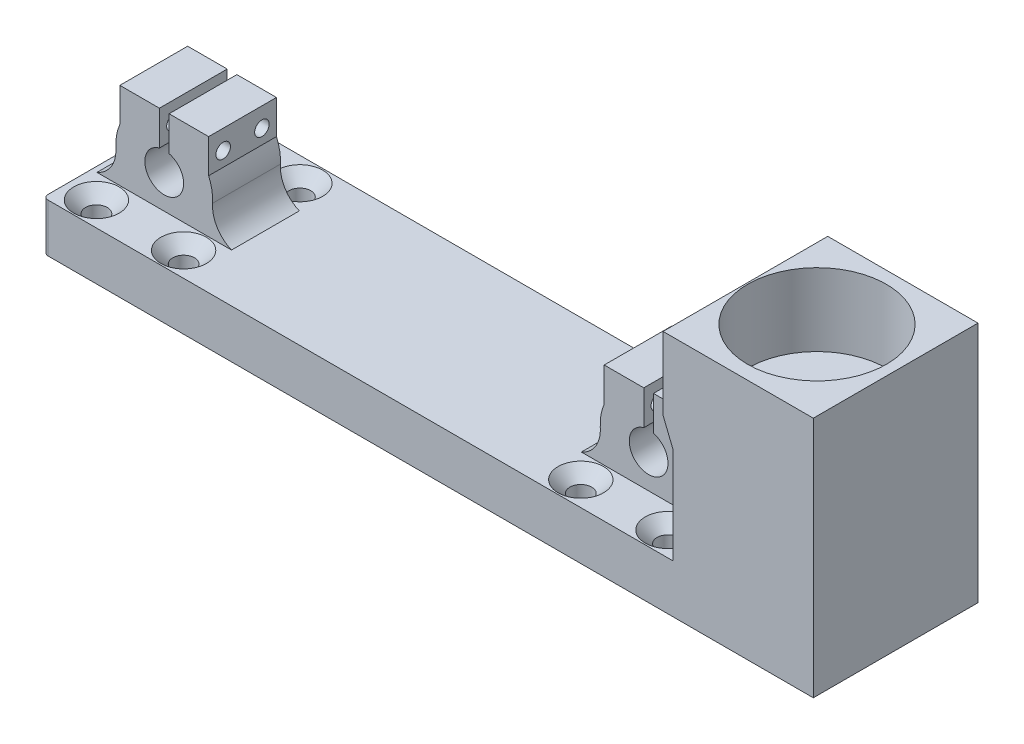
SolidWorks part; units mm, degrees
ref_plane "Front Plane" through (0, 0, 0) normal (0, 0, 1) x (1, 0, 0)
ref_plane "Top Plane" through (0, 0, 0) normal (0, 1, 0) x (1, 0, 0)
ref_plane "Right Plane" through (0, 0, 0) normal (1, 0, 0) x (0, 0, -1)
sketch "Sketch1" plane through (0, 0, 0) normal (0, 1, 0) x (1, 0, 0)
  line B0 (-24, -29) -> (6, -29)
  line B1 (6, 5) -> (6, -29)
  line B2 (-24, 5) -> (-24, -29)
  line B3 (-24, 5) -> (6, 5)
  circle B4 centre (0, -24) radius 2
  circle B5 centre (-18, -24) radius 2
  circle B6 centre (-18, 0) radius 2
  circle B7 centre (0, 0) radius 2
sketch_block_instance "Block-LinearBearing-1"
sketch_block "Block-LinearBearing"
sketch "Sketch2" plane through (0, 0, 0) normal (0, 1, 0) x (1, 0, 0)
  line L0 (-24, -29) -> (6, -29) construction
  line L1 (6, 5) -> (6, -29) construction
  line L2 (-24, 5) -> (-24, -29) construction
  line L3 (-24, 5) -> (6, 5) construction
  line L4 (-24, -29) -> (6, -29)
  line L5 (6, 5) -> (6, -29)
  line L6 (-24, 5) -> (-24, -29)
  line L7 (-24, 5) -> (6, 5)
  line L8 (6, 5) -> (41, 5)
  line L9 (41, 5) -> (41, -29)
  line L10 (41, -29) -> (6, -29)
  circle A0 centre (0, 0) radius 2 construction
  circle A1 centre (-18, 0) radius 2 construction
  circle A2 centre (-18, -24) radius 2 construction
  circle A3 centre (0, -24) radius 2 construction
  circle A4 centre (0, 0) radius 2
  circle A5 centre (-18, 0) radius 2
  circle A6 centre (-18, -24) radius 2
  circle A7 centre (0, -24) radius 2
  dimension "D1" = 35
extrude "Boss-Extrude1" add sketch "Sketch2" along normal blind 10 contours L10 L9 L8 L5 | L7 L6 L4 L5 A7 A6 A5 A4
fillet "Fillet1" radius 1 2 edges at (-24, 5, 29) (-24, 5, -5)
ref_plane "Plane1" through (0, 0, 19) normal (0, 0, 1) x (1, 0, 0)
sketch "Sketch3" plane through (0, 0, 19) normal (0, 0, 1) x (1, 0, 0)
  line L0 (-24, 0) -> (-24, 10) construction
  line L2 (-22.8852, 10) -> (4.8852, 10)
  line L3 (-9, 20.9227) -> (0.1652, 20.9227) construction
  line L4 (-9, 20.9227) -> (-18.1652, 20.9227) construction
  line L5 (-18.1652, 20.9227) -> (-18.1652, 27.9232)
  line L6 (-18.1652, 27.9232) -> (0.1652, 27.9232)
  line L7 (0.1652, 27.9232) -> (0.1652, 20.9227)
  circle A0 centre (-9, 16.9227) radius 4
  arc A2 (-19.0471, 16.9227) -> (-22.8852, 10) centre (-25.3926, 15.9155) cw
  arc A3 (1.0471, 16.9227) -> (4.8852, 10) centre (7.3926, 15.9155) ccw
  arc A4 (0.9741, 16.2033) -> (0.1652, 20.9227) centre (-9, 16.9227) ccw
  arc A5 (-18.1652, 20.9227) -> (-18.9741, 16.2033) centre (-9, 16.9227) ccw
  point P0 (-9, 10)
  dimension "D1" = 8
  dimension "D2" = 6
  dimension "D3" = 15
hole_wizard "CSK for M4 Flat Head Machine Screw1" positions "Sketch4" profile "Sketch5" countersink size "M4" standard "ANSI Metric" end condition up to next
sketch "Sketch4" plane through (0, 10, 0) normal (0, 1, 0) x (1, 0, 0)
  point P21 (-18, 0)
  point P24 (0, 0)
  point P27 (0, -24)
  point P30 (-18, -24)
sketch "Sketch5" plane through (-18, 10, 0) normal (1, 0, 0) x (0, 0, 1)
  line L0 (0, 0) -> (0, 10)
  line L1 (0, 10) -> (2.25, 10)
  line L2 (2.25, 10) -> (2.25, 2.45)
  line L3 (2.25, 2.45) -> (4.7, 0)
  line L5 (4.7, 0) -> (0, 0)
  line L6 (-2.25, 2.45) -> (-4.7, 0) construction
  line L11 (0, -6.35) -> (0, 107.95) construction
  dimension "Thru Hole Dia." = 4.5
  dimension "Thru Hole Depth" = 10
  dimension "Near C'Sink Dia." = 9.4
  dimension "Near C'Sink Angle" = 90
extrude "Boss-Extrude2" add sketch "Sketch3" against normal offset from surface (14 mm away) 10
hole_wizard "Ø3.0mm Dowel Hole1" positions "Sketch8" profile "Sketch9" hole size "Ø3.0" standard "ANSI Metric" end condition up to next
sketch "Sketch8" plane through (0.1652, 0, 0) normal (1, 0, 0) x (0, 0, -1)
  line L0 (-19, 27.9232) -> (-19, 20.9227) construction
  line L1 (-5, 20.9227) -> (-5, 27.9232) construction
  line L2 (-5, 27.9232) -> (-19, 27.9232) construction
  point P0 (-16, 23.9232)
  point P2 (-8, 23.9232)
  dimension "D1" = 3
  dimension "D2" = 3
  dimension "D3" = 4
  dimension "D4" = 4
sketch "Sketch9" plane through (0.1652, 23.9232, 16) normal (0, 1, 0) x (0, 0, -1)
  line L0 (0, 0) -> (0, 18.3303)
  line L1 (0, 18.3303) -> (1.5, 18.3303)
  line L2 (1.5, 18.3303) -> (1.5, 0)
  line L5 (1.5, 0) -> (0, 0)
  line L11 (0, -6.35) -> (0, 107.95) construction
  dimension "Thru Hole Dia." = 3
  dimension "Thru Hole Depth" = 18.3303
sketch "Sketch10" plane through (0, 0, 19) normal (0, 0, 1) x (1, 0, 0)
  line L0 (-10, 27.9232) -> (-8, 27.9232)
  line L1 (-18.1652, 27.9232) -> (0.1652, 27.9232) construction
  line L2 (-8, 27.9232) -> (-8, 20.7957)
  line L3 (-9, 27.9232) -> (-9, 20.9227)
  line L4 (-10, 27.9232) -> (-10, 20.7957)
  circle A0 centre (-9, 16.9227) radius 4 construction
  arc A1 (-8, 20.7957) -> (-10, 20.7957) centre (-9, 16.9227) ccw
  circle M5 centre (-9, 16.9227) radius 4
  line M13 (0.1652, 27.9232) -> (-18.1652, 27.9232)
  dimension "D1" = 1
extrude "Cut-Extrude1" cut sketch "Sketch10" against normal through all contours L0 L4 L3 M5 | L3 L2 M13 M5
mirror "Mirror11" about plane through (41, 10, 0) normal (1, 0, 0) of "Ø3.0mm Dowel Hole1", "Boss-Extrude1", "Boss-Extrude2", "Cut-Extrude1", "CSK for M4 Flat Head Machine Screw1"
hole_wizard "CSK for M3 Flat Head Machine Screw1" positions "Sketch13" profile "Sketch14" countersink size "M3" standard "ANSI Metric"
sketch "Sketch13" plane through (0, 0, -5) normal (0, 0, -1) x (-1, 0, 0)
  line L0 (23, 10) -> (-106, 10) construction
  line L3 (-41.5, 10) -> (-41.5, 0) construction
  line L4 (23, 0) -> (-106, 0) construction
  point P4 (-69.1148, 5)
  point P6 (-59.1148, 5)
  point P31 (-13.8852, 5)
  point P32 (-23.8852, 5)
  dimension "D1" = 5
  dimension "D2" = 8
  dimension "D3" = 10
  dimension "D4" = 5
sketch "Sketch14" plane through (69.1148, 5, -5) normal (1, 0, 0) x (0, 1, 0)
  line L0 (0, 0) -> (0, 11.0215)
  line L1 (0, 11.0215) -> (1.7, 10)
  line L2 (1.7, 10) -> (1.7, 1.45)
  line L3 (1.7, 1.45) -> (3.15, 0)
  line L5 (3.15, 0) -> (0, 0)
  line L6 (-1.7, 1.45) -> (-3.15, 0) construction
  line L10 (0, 11.0215) -> (-1.7, 10) construction
  line L11 (0, -6.35) -> (0, 107.95) construction
  dimension "Hole Dia." = 3.4
  dimension "Hole Depth" = 10
  dimension "Near C'Sink Dia." = 6.3
  dimension "Near C'Sink Angle" = 90
  dimension "Drill Angle" = 118
ref_plane "Plane2" through (0, 5, 0) normal (0, -1, 0) x (-1, 0, 0)
sketch "Sketch15" plane through (0, 0, 0) normal (0, 1, 0) x (1, 0, 0)
  line L0 (106, -29) -> (-23, -29) construction
  line L1 (106, 5) -> (135, 5)
  line L2 (106, 5) -> (106, -29)
  line L3 (106, -29) -> (135, -29)
  line L4 (135, 5) -> (135, -29)
  circle A0 centre (118.7965, -11.3259) radius 14.2875 construction
  dimension "D2" = 28.575
  dimension "D1" = 29
extrude "Boss-Extrude3" add sketch "Sketch15" along normal blind 35
sketch "Sketch16" plane through (0, 35, 0) normal (0, 1, 0) x (1, 0, 0)
  line L4 (103.9825, -29) -> (135, -29)
  line L5 (106, -29) -> (-23, -29) construction
  line L6 (135, -29) -> (135, 5)
  line L7 (135, 5) -> (103.9825, 5)
  line L8 (-23, 5) -> (106, 5) construction
  line L9 (103.9825, 5) -> (103.9825, -11.839)
  line L10 (103.9825, -11.839) -> (103.9825, -29)
  line L11 (-24, 5) -> (-24, -29) construction
  circle A0 centre (118.6, -11.839) radius 14.325
  point P2 (0, 0)
  point P3 (0, 0)
  point P9 (103.9825, -11.839)
  point P16 (0, 0)
  dimension "D2" = 28.65
  dimension "D1" = 142.6
extrude "Boss-Extrude4" add sketch "Sketch16" along normal blind 15
sketch "Sketch17" plane through (0, 0, 29) normal (0, 0, 1) x (1, 0, 0)
  line L0 (103.9825, 35) -> (106, 30)
  line L1 (106, 35) -> (106, 10) construction
  line L2 (103.9825, 35) -> (106, 35)
  line L3 (106, 35) -> (106, 30)
  point P5 (106, 30.4551)
  dimension "D1" = 5
extrude "Boss-Extrude5" add sketch "Sketch17" against normal up to surface (34 mm away) up to face at (65.9648, 5, -5)
equation "\"middlewidth\"= 70"
equation "\"D1@Sketch2\"=\"middlewidth\"/2"
